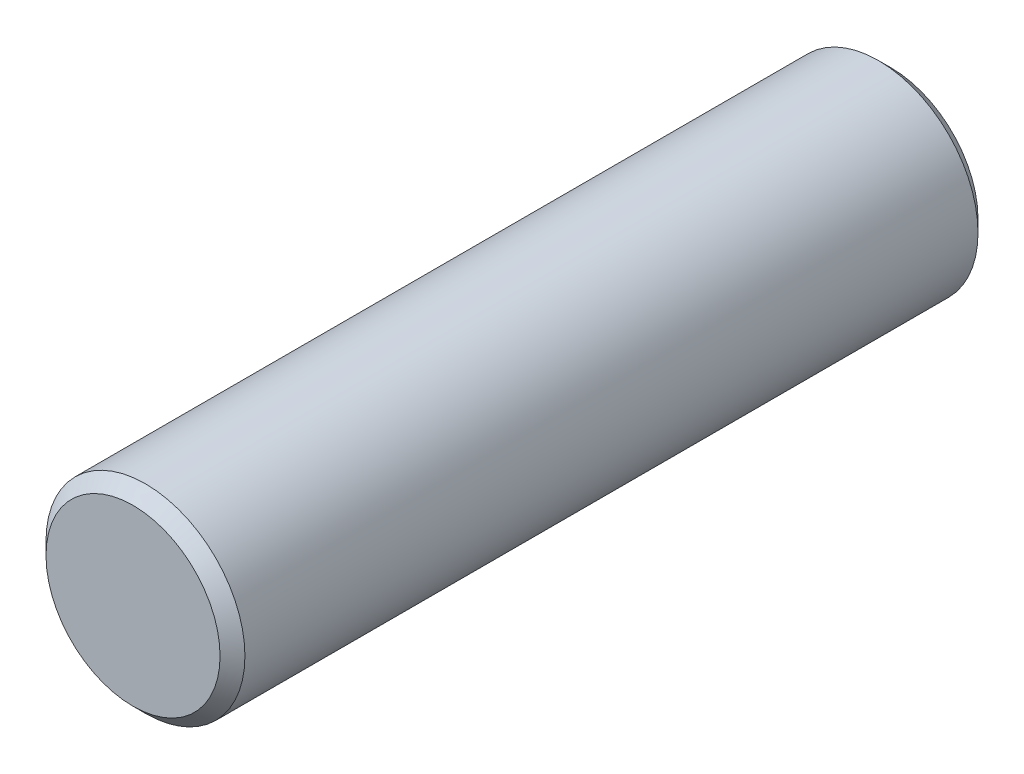
SolidWorks part; units mm, degrees
ref_plane "Front Plane" through (0, 0, 0) normal (0, 0, 1) x (1, 0, 0)
ref_plane "Top Plane" through (0, 0, 0) normal (0, 1, 0) x (1, 0, 0)
ref_plane "Right Plane" through (0, 0, 0) normal (1, 0, 0) x (0, 0, -1)
sketch "Sketch1" plane through (0, 0, 0) normal (0, 0, 1) x (1, 0, 0)
  circle A0 centre (0, 0) radius 4
  dimension "D1" = 8
extrude "Boss-Extrude1" add sketch "Sketch1" along normal blind 30.48
chamfer "Chamfer1" distance 0.5 angle 45 2 edges at (4, 0, 0) (4, 0, 30.48)
